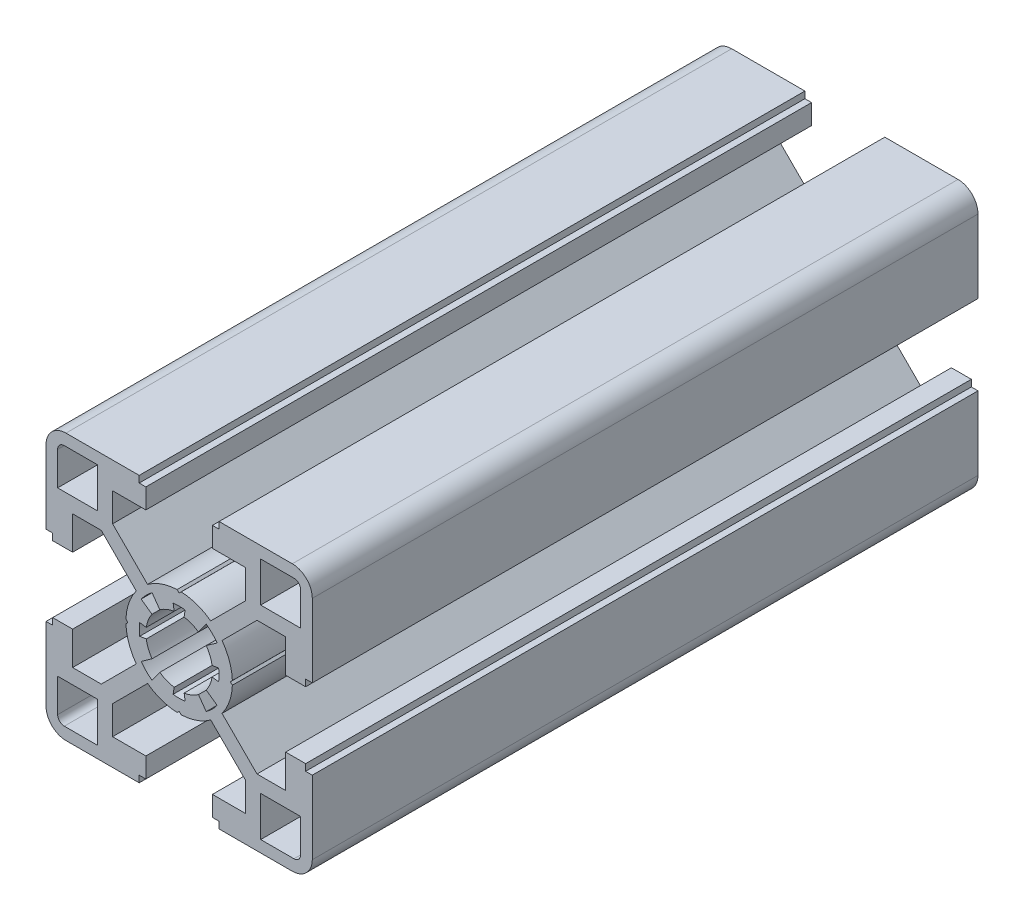
SolidWorks part; units mm, degrees
ref_plane "Ön Düzlem" through (0, 0, 0) normal (0, 0, 1) x (1, 0, 0)
ref_plane "Üst Düzlem" through (0, 0, 0) normal (0, 1, 0) x (1, 0, 0)
ref_plane "Sağ Düzlem" through (0, 0, 0) normal (1, 0, 0) x (0, 0, -1)
ref_plane "Düzlem1" through (0, 0, 100) normal (0, 0, 1) x (1, 0, 0)
sketch "Çizim1" plane through (0, 0, 100) normal (0, 0, 1) x (1, 0, 0)
  line L0 (18.25, 12.25) -> (12.25, 12.25)
  line L1 (12.25, 12.25) -> (12.25, 18.25)
  line L2 (12.25, 18.25) -> (17.25, 18.25)
  line L3 (18.25, 17.25) -> (18.25, 12.25)
  line L4 (-18.25, -12.25) -> (-12.25, -12.25)
  line L5 (-12.25, -12.25) -> (-12.25, -18.25)
  line L6 (-12.25, -18.25) -> (-17.25, -18.25)
  line L7 (-18.25, -17.25) -> (-18.25, -12.25)
  line L8 (6, -19) -> (6, -20)
  line L9 (6, -20) -> (17, -20)
  line L10 (20, -17) -> (20, -6)
  line L11 (20, -6) -> (19, -6)
  line L12 (19, -6) -> (19, -5)
  line L13 (19, -5) -> (16, -5)
  line L14 (16, -5) -> (16, -10)
  line L15 (16, -10) -> (11.6971, -10)
  line L16 (11.6971, -10) -> (6.4414, -4.7443)
  line L17 (7.9941, -0.3064) -> (7.7, 0)
  line L18 (7.7, 0) -> (7.9941, 0.3064)
  line L19 (6.4414, 4.7443) -> (11.6971, 10)
  line L20 (11.6971, 10) -> (16, 10)
  line L21 (16, 10) -> (16, 5)
  line L22 (16, 5) -> (19, 5)
  line L23 (19, 5) -> (19, 6)
  line L24 (19, 6) -> (20, 6)
  line L25 (20, 6) -> (20, 17)
  line L26 (17, 20) -> (6, 20)
  line L27 (6, 20) -> (6, 19)
  line L28 (6, 19) -> (5, 19)
  line L29 (5, 19) -> (5, 16)
  line L30 (5, 16) -> (10, 16)
  line L31 (10, 16) -> (10, 11.6971)
  line L32 (10, 11.6971) -> (4.7443, 6.4414)
  line L33 (0.3064, 7.9941) -> (0, 7.7)
  line L34 (0, 7.7) -> (-0.3064, 7.9941)
  line L35 (-4.7443, 6.4414) -> (-10, 11.6971)
  line L36 (-10, 11.6971) -> (-10, 16)
  line L37 (-10, 16) -> (-5, 16)
  line L38 (-5, 16) -> (-5, 19)
  line L39 (-5, 19) -> (-6, 19)
  line L40 (-6, 19) -> (-6, 20)
  line L41 (-6, 20) -> (-17, 20)
  line L42 (-20, 17) -> (-20, 6)
  line L43 (-20, 6) -> (-19, 6)
  line L44 (-19, 6) -> (-19, 5)
  line L45 (-19, 5) -> (-16, 5)
  line L46 (-16, 5) -> (-16, 10)
  line L47 (-16, 10) -> (-11.6971, 10)
  line L48 (-11.6971, 10) -> (-6.4414, 4.7443)
  line L49 (-7.9941, 0.3064) -> (-7.7, 0)
  line L50 (-7.7, 0) -> (-7.9941, -0.3064)
  line L51 (-6.4414, -4.7443) -> (-11.6971, -10)
  line L52 (-11.6971, -10) -> (-16, -10)
  line L53 (-16, -10) -> (-16, -5)
  line L54 (-16, -5) -> (-19, -5)
  line L55 (-19, -5) -> (-19, -6)
  line L56 (-19, -6) -> (-20, -6)
  line L57 (-20, -6) -> (-20, -17)
  line L58 (-17, -20) -> (-6, -20)
  line L59 (-6, -20) -> (-6, -19)
  line L60 (-6, -19) -> (-5, -19)
  line L61 (-5, -19) -> (-5, -16)
  line L62 (-5, -16) -> (-10, -16)
  line L63 (-10, -16) -> (-10, -11.6971)
  line L64 (-10, -11.6971) -> (-4.7443, -6.4414)
  line L65 (-0.3064, -7.9941) -> (0, -7.7)
  line L66 (0, -7.7) -> (0.3064, -7.9941)
  line L67 (4.7443, -6.4414) -> (10, -11.6971)
  line L68 (10, -11.6971) -> (10, -16)
  line L69 (10, -16) -> (5, -16)
  line L70 (5, -16) -> (5, -19)
  line L71 (5, -19) -> (6, -19)
  line L72 (-12.25, 18.25) -> (-12.25, 12.25)
  line L73 (-12.25, 12.25) -> (-18.25, 12.25)
  line L74 (-18.25, 12.25) -> (-18.25, 17.25)
  line L75 (-17.25, 18.25) -> (-12.25, 18.25)
  line L76 (12.25, -18.25) -> (12.25, -12.25)
  line L77 (12.25, -12.25) -> (18.25, -12.25)
  line L78 (18.25, -12.25) -> (18.25, -17.25)
  line L79 (17.25, -18.25) -> (12.25, -18.25)
  line L80 (-5.7057, -4.0552) -> (-4.0755, -2.8966)
  line L81 (-4.9435, -0.7494) -> (-5.9322, -0.8993)
  line L82 (-5.9322, 0.8993) -> (-4.9435, 0.7494)
  line L83 (-4.0755, 2.8966) -> (-5.7057, 4.0552)
  line L84 (-4.0641, 5.6994) -> (-2.903, 4.071)
  line L85 (-0.7494, 4.9435) -> (-0.8993, 5.9322)
  line L86 (0.8993, 5.9322) -> (0.7494, 4.9435)
  line L87 (2.903, 4.071) -> (4.0641, 5.6994)
  line L88 (5.7057, 4.0552) -> (4.0755, 2.8966)
  line L89 (4.9435, 0.7494) -> (5.9322, 0.8993)
  line L90 (5.9322, -0.8993) -> (4.9435, -0.7494)
  line L91 (4.0755, -2.8966) -> (5.7057, -4.0552)
  line L92 (4.0641, -5.6994) -> (2.903, -4.071)
  line L93 (0.7494, -4.9435) -> (0.8993, -5.9322)
  line L94 (-0.8993, -5.9322) -> (-0.7494, -4.9435)
  line L95 (-2.903, -4.071) -> (-4.0641, -5.6994)
  arc A0 (17.25, 18.25) -> (18.25, 17.25) centre (17.25, 17.25) cw
  arc A1 (-17.25, -18.25) -> (-18.25, -17.25) centre (-17.25, -17.25) cw
  arc A2 (17, -20) -> (20, -17) centre (17, -17) ccw
  arc A3 (6.4414, -4.7443) -> (7.9941, -0.3064) centre (0, 0) ccw
  arc A4 (7.9941, 0.3064) -> (6.4414, 4.7443) centre (0, 0) ccw
  arc A5 (20, 17) -> (17, 20) centre (17, 17) ccw
  arc A6 (4.7443, 6.4414) -> (0.3064, 7.9941) centre (0, 0) ccw
  arc A7 (-0.3064, 7.9941) -> (-4.7443, 6.4414) centre (0, 0) ccw
  arc A8 (-17, 20) -> (-20, 17) centre (-17, 17) ccw
  arc A9 (-6.4414, 4.7443) -> (-7.9941, 0.3064) centre (0, 0) ccw
  arc A10 (-7.9941, -0.3064) -> (-6.4414, -4.7443) centre (0, 0) ccw
  arc A11 (-20, -17) -> (-17, -20) centre (-17, -17) ccw
  arc A12 (-4.7443, -6.4414) -> (-0.3064, -7.9941) centre (0, 0) ccw
  arc A13 (0.3064, -7.9941) -> (4.7443, -6.4414) centre (0, 0) ccw
  arc A14 (-18.25, 17.25) -> (-17.25, 18.25) centre (-17.25, 17.25) cw
  arc A15 (18.25, -17.25) -> (17.25, -18.25) centre (17.25, -17.25) cw
  arc A16 (-4.0641, -5.6994) -> (-5.7057, -4.0552) centre (0, 0) cw
  arc A17 (-4.0755, -2.8966) -> (-4.9435, -0.7494) centre (0, 0) cw
  arc A18 (-5.9322, -0.8993) -> (-5.9322, 0.8993) centre (0, 0) cw
  arc A19 (-4.9435, 0.7494) -> (-4.0755, 2.8966) centre (0, 0) cw
  arc A20 (-5.7057, 4.0552) -> (-4.0641, 5.6994) centre (0, 0) cw
  arc A21 (-2.903, 4.071) -> (-0.7494, 4.9435) centre (0, 0) cw
  arc A22 (-0.8993, 5.9322) -> (0.8993, 5.9322) centre (0, 0) cw
  arc A23 (0.7494, 4.9435) -> (2.903, 4.071) centre (0, 0) cw
  arc A24 (4.0641, 5.6994) -> (5.7057, 4.0552) centre (0, 0) cw
  arc A25 (4.0755, 2.8966) -> (4.9435, 0.7494) centre (0, 0) cw
  arc A26 (5.9322, 0.8993) -> (5.9322, -0.8993) centre (0, 0) cw
  arc A27 (4.9435, -0.7494) -> (4.0755, -2.8966) centre (0, 0) cw
  arc A28 (5.7057, -4.0552) -> (4.0641, -5.6994) centre (0, 0) cw
  arc A29 (2.903, -4.071) -> (0.7494, -4.9435) centre (0, 0) cw
  arc A30 (0.8993, -5.9322) -> (-0.8993, -5.9322) centre (0, 0) cw
  arc A31 (-0.7494, -4.9435) -> (-2.903, -4.071) centre (0, 0) cw
extrude "Yükseklik-Ekstrüzyon1" add sketch "Çizim1" against normal blind 100
